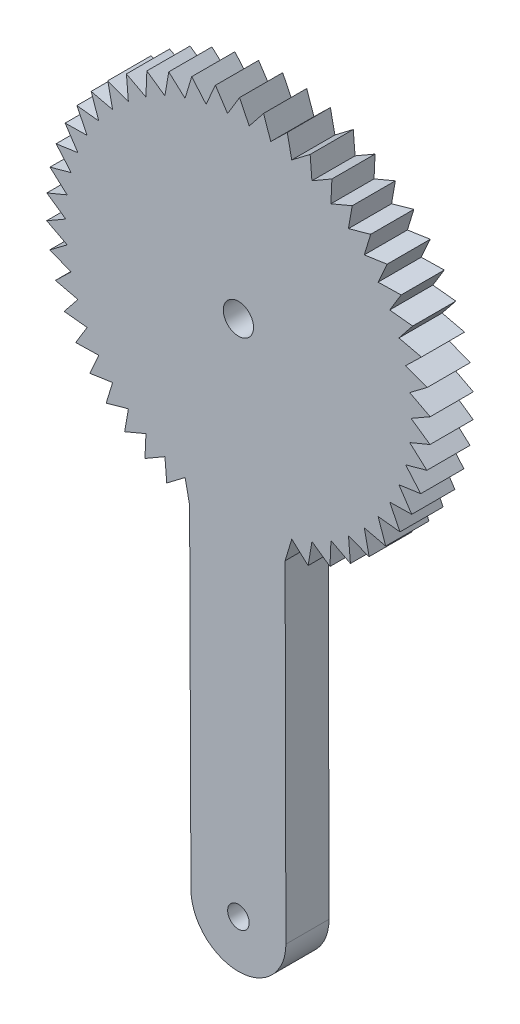
SolidWorks part; units mm, degrees
ref_plane "Front Plane" through (0, 0, 0) normal (0, 0, 1) x (1, 0, 0)
ref_plane "Top Plane" through (0, 0, 0) normal (0, 1, 0) x (1, 0, 0)
ref_plane "Right Plane" through (0, 0, 0) normal (1, 0, 0) x (0, 0, -1)
sketch "Sketch1" plane through (0, 0, 0) normal (0, 0, 1) x (1, 0, 0)
  line L0 (385.2934, 338.8605) -> (383.9081, 336.5711)
  line L2 (386.4197, 336.5715) -> (385.2934, 338.8605)
  line L3 (388.081, 338.6692) -> (386.4197, 336.5715)
  line L50 (388.9116, 336.2571) -> (388.081, 338.6692)
  line L51 (390.8226, 338.13) -> (388.9116, 336.2571)
  line L52 (391.3444, 335.6328) -> (390.8226, 338.13)
  line L53 (393.4751, 337.2515) -> (391.3444, 335.6328)
  line L54 (393.6797, 334.7085) -> (393.4751, 337.2515)
  line L55 (395.9965, 336.0474) -> (393.6797, 334.7085)
  line L56 (395.8808, 333.4989) -> (395.9965, 336.0474)
  line L57 (398.3472, 334.5368) -> (395.8808, 333.4989)
  line L105 (397.913, 332.0229) -> (398.3472, 334.5368)
  line L106 (400.49, 332.7435) -> (397.913, 332.0229)
  line L107 (399.7441, 330.3038) -> (400.49, 332.7435)
  line L108 (402.3911, 330.6958) -> (399.7441, 330.3038)
  line L109 (401.3453, 328.3688) -> (402.3911, 330.6958)
  line L110 (404.0206, 328.4259) -> (401.3453, 328.3688)
  line L111 (402.6914, 326.2484) -> (404.0206, 328.4259)
  line L112 (405.3527, 325.9697) -> (402.6914, 326.2484)
  line L114 (379.5108, 295.0918) -> (379.6667, 256.6109)
  line L115 (390.6667, 256.6109) -> (390.5773, 295.0288)
  line L121 (403.7611, 323.976) -> (405.3527, 325.9697)
  line L122 (406.3665, 323.366) -> (403.7611, 323.976)
  line L123 (404.5376, 321.5874) -> (406.3665, 323.366)
  line L124 (407.046, 320.6557) -> (404.5376, 321.5874)
  line L125 (405.0086, 319.1203) -> (407.046, 320.6557)
  line L126 (407.3804, 317.8816) -> (405.0086, 319.1203)
  line L127 (405.1666, 316.6137) -> (407.3804, 317.8816)
  line L128 (407.3645, 315.0874) -> (405.1666, 316.6137)
  line L129 (405.0093, 314.107) -> (407.3645, 315.0874)
  line L130 (406.9985, 312.3173) -> (405.0093, 314.107)
  line L131 (404.539, 311.6398) -> (406.9985, 312.3173)
  line L132 (406.2883, 309.6149) -> (404.539, 311.6398)
  line L133 (403.7632, 309.2511) -> (406.2883, 309.6149)
  line L134 (405.2449, 307.0229) -> (403.7632, 309.2511)
  line L135 (402.6941, 306.9783) -> (405.2449, 307.0229)
  line L136 (403.8849, 304.582) -> (402.6941, 306.9783)
  line L137 (401.3486, 304.8575) -> (403.8849, 304.582)
  line L138 (402.2297, 302.3309) -> (401.3486, 304.8575)
  line L139 (399.748, 302.9221) -> (402.2297, 302.3309)
  line L140 (400.3053, 300.3049) -> (399.748, 302.9221)
  line L141 (397.9173, 301.2025) -> (400.3053, 300.3049)
  line L142 (398.1423, 298.5361) -> (397.9173, 301.2025)
  line L143 (395.8856, 299.7259) -> (398.1423, 298.5361)
  line L144 (395.7746, 297.0524) -> (395.8856, 299.7259)
  line L145 (393.6848, 298.5156) -> (395.7746, 297.0524)
  line L146 (393.2396, 295.8771) -> (393.6848, 298.5156)
  line L147 (391.3497, 297.5907) -> (393.2396, 295.8771)
  line L148 (390.5773, 295.0288) -> (391.3497, 297.5907)
  line L149 (378.9891, 297.589) -> (379.5108, 295.0918)
  line L150 (376.8584, 295.9703) -> (378.9891, 297.589)
  line L151 (376.6537, 298.5132) -> (376.8584, 295.9703)
  line L152 (374.3369, 297.1744) -> (376.6537, 298.5132)
  line L153 (374.4526, 299.7229) -> (374.3369, 297.1744)
  line L154 (371.9863, 298.685) -> (374.4526, 299.7229)
  line L155 (372.4205, 301.1989) -> (371.9863, 298.685)
  line L156 (369.8435, 300.4783) -> (372.4205, 301.1989)
  line L157 (370.5894, 302.918) -> (369.8435, 300.4783)
  line L158 (367.9424, 302.526) -> (370.5894, 302.918)
  line L159 (368.9881, 304.853) -> (367.9424, 302.526)
  line L160 (366.3129, 304.7959) -> (368.9881, 304.853)
  line L161 (367.642, 306.9734) -> (366.3129, 304.7959)
  line L162 (364.9807, 307.252) -> (367.642, 306.9734)
  line L163 (366.5723, 309.2458) -> (364.9807, 307.252)
  line L164 (363.9669, 309.8558) -> (366.5723, 309.2458)
  line L165 (365.7959, 311.6344) -> (363.9669, 309.8558)
  line L166 (363.2875, 312.5661) -> (365.7959, 311.6344)
  line L167 (365.3249, 314.1014) -> (363.2875, 312.5661)
  line L168 (362.953, 315.3402) -> (365.3249, 314.1014)
  line L169 (365.1668, 316.6081) -> (362.953, 315.3402)
  line L170 (362.9689, 318.1343) -> (365.1668, 316.6081)
  line L171 (365.3242, 319.1147) -> (362.9689, 318.1343)
  line L172 (363.3349, 320.9044) -> (365.3242, 319.1147)
  line L173 (365.7945, 321.5819) -> (363.3349, 320.9044)
  line L174 (364.0452, 323.6068) -> (365.7945, 321.5819)
  line L175 (366.5703, 323.9707) -> (364.0452, 323.6068)
  line L176 (365.0886, 326.1989) -> (366.5703, 323.9707)
  line L177 (367.6393, 326.2434) -> (365.0886, 326.1989)
  line L178 (366.4486, 328.6398) -> (367.6393, 326.2434)
  line L179 (368.9848, 328.3642) -> (366.4486, 328.6398)
  line L180 (368.1038, 330.8909) -> (368.9848, 328.3642)
  line L181 (370.5855, 330.2997) -> (368.1038, 330.8909)
  line L182 (370.0281, 332.9169) -> (370.5855, 330.2997)
  line L183 (372.4161, 332.0193) -> (370.0281, 332.9169)
  line L184 (372.1912, 334.6857) -> (372.4161, 332.0193)
  line L185 (374.4479, 333.4958) -> (372.1912, 334.6857)
  line L186 (374.5589, 336.1694) -> (374.4479, 333.4958)
  line L187 (376.6486, 334.7061) -> (374.5589, 336.1694)
  line L188 (377.0938, 337.3447) -> (376.6486, 334.7061)
  line L189 (378.9837, 335.631) -> (377.0938, 337.3447)
  line L190 (379.7561, 338.193) -> (378.9837, 335.631)
  line L191 (381.4164, 336.256) -> (379.7561, 338.193)
  line L192 (382.5037, 338.701) -> (381.4164, 336.256)
  line L193 (383.9081, 336.5711) -> (382.5037, 338.701)
  circle A48 centre (385.1667, 316.6109) radius 1.75
  arc A49 (379.6667, 256.6109) -> (390.6667, 256.6365) centre (385.1667, 256.6109) ccw
  circle A50 centre (385.1667, 256.6109) radius 1.25
  point P143 (385.1667, 316.6109)
  dimension "D3" = 3.5
  dimension "D4" = 22.25
  dimension "D7" = 22.25
  dimension "D6" = 22.25
  dimension "D5" = 19.9999
sketch3d "3DSketch1" plane through (0, 0, 0) normal (0, 0, 1) x (1, 0, 0)
extrude "Boss-Extrude2" add sketch "Sketch1" along normal blind 5 contours L114 A49 L115 L148 L147 L146 L145 L144 L143 L142 L141 L140 L139 L138 L137 L136 L135 L134 L133 L132 L131 L130 L129 L128 L127 L126 L125 L124 L123 L122 L121 L112 L111 L110 L109 L108 L107 L106 L105 L57 L56 L55 L54 L53 L52 L51 L50 L3 L2 L0
